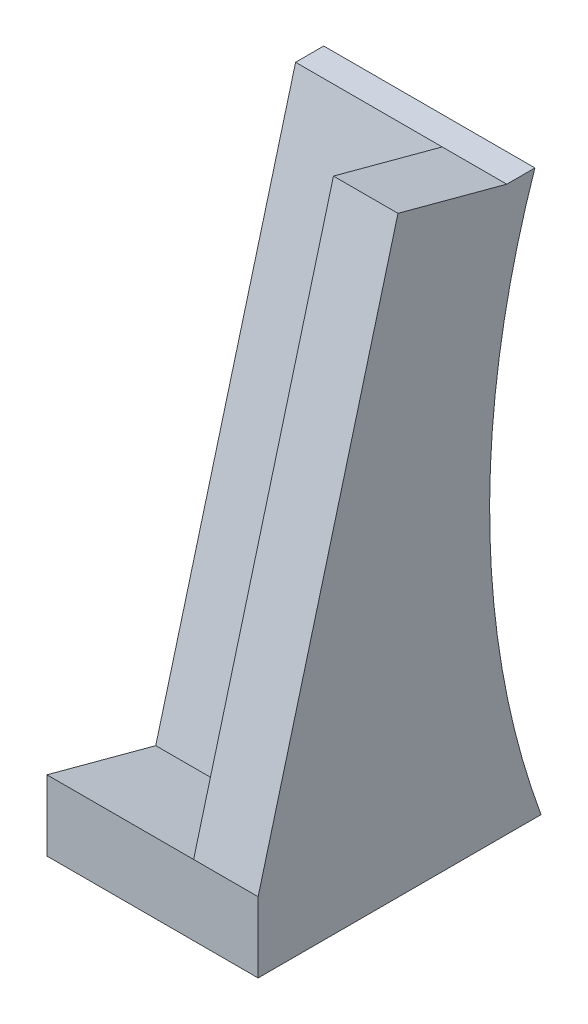
SolidWorks part; units mm, degrees
ref_plane "Front Plane" through (0, 0, 0) normal (0, 0, 1) x (1, 0, 0)
ref_plane "Top Plane" through (0, 0, 0) normal (0, 1, 0) x (1, 0, 0)
ref_plane "Right Plane" through (0, 0, 0) normal (1, 0, 0) x (0, 0, -1)
sketch "Sketch1" plane through (0, 0, 0) normal (1, 0, 0) x (0, 0, -1)
  line L0 (0, 0) -> (51.0442, 0)
  line L1 (0, 12.7) -> (0, 0)
  line L2 (0, 12.7) -> (19.6276, 7.4408)
  line L3 (19.6276, 7.4408) -> (44.8575, 101.6)
  line L4 (44.8575, 101.6) -> (49.9375, 101.6)
  arc A1 (49.9375, 101.6) -> (51.0442, 0) centre (194.1654, 52.3651) ccw
  dimension "D1" = 90
  dimension "D6" = 152.4
  dimension "D2" = 12.7
  dimension "D3" = 20.32
  dimension "D4" = 75
  dimension "D5" = 101.6
  dimension "D7" = 5.08
  dimension "D8" = 52.3651
extrude "Boss-Extrude1" add sketch "Sketch1" along normal blind 38.1
sketch "Sketch2" plane through (0, -4.4085, -16.4526) normal (0, 0.2588, 0.9659) x (1, 0, 0)
  line L0 (38.1, 109.748) -> (0, 109.748) construction
  line L1 (26.4595, 109.748) -> (38.1, 109.748)
  line L2 (26.4595, 109.748) -> (26.4595, 12.2673)
  line L3 (26.4595, 12.2673) -> (38.1, 12.2673)
  line L4 (38.1, 109.748) -> (38.1, 12.2673)
extrude "Boss-Extrude2" add sketch "Sketch2" along normal blind 20.32
